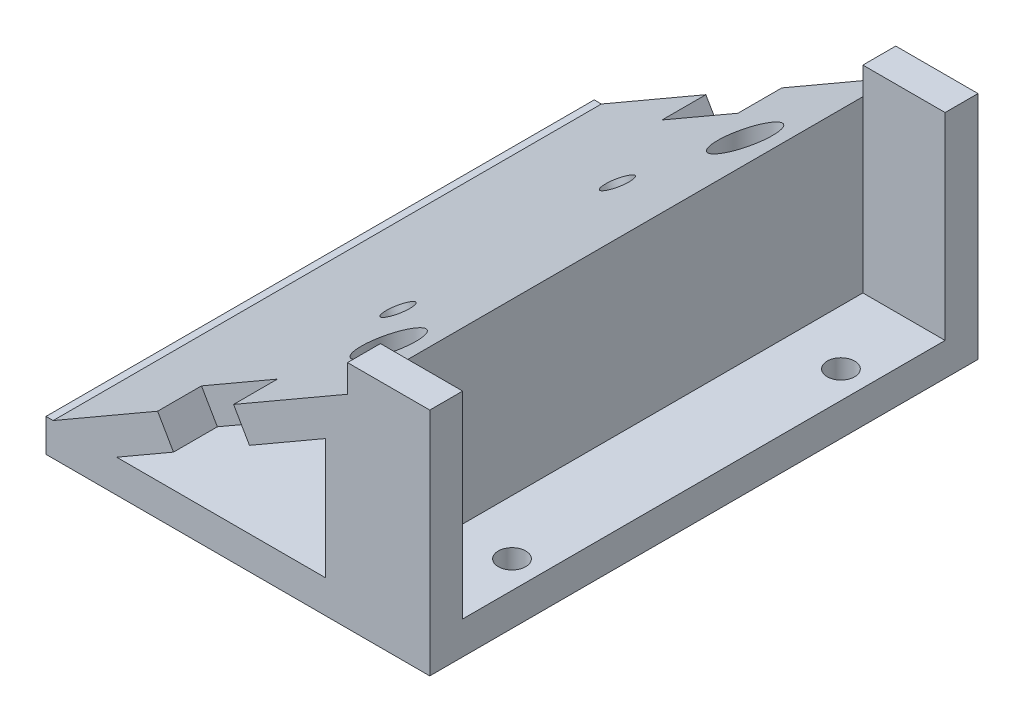
SolidWorks part; units mm, degrees
ref_plane "Front Plane" through (0, 0, 0) normal (0, 0, 1) x (1, 0, 0)
ref_plane "Top Plane" through (0, 0, 0) normal (0, 1, 0) x (1, 0, 0)
ref_plane "Right Plane" through (0, 0, 0) normal (1, 0, 0) x (0, 0, -1)
sketch "Sketch1" plane through (0, 0, 0) normal (0, 1, 0) x (1, 0, 0)
  line L1 (-70.1234, 23.0109) -> (-105.1234, 23.0109)
  line L2 (-70.1234, 23.0109) -> (-70.1234, 73.0109)
  line L3 (-70.1234, 73.0109) -> (-105.1234, 73.0109)
  line L4 (-105.1234, 23.0109) -> (-105.1234, 73.0109)
  dimension "D1" = 50
  dimension "D2" = 35
extrude "Boss-Extrude1" add sketch "Sketch1" along normal blind 3
sketch "Sketch2" plane through (0, 3, 0) normal (0, 1, 0) x (1, 0, 0)
  line L0 (-70.1234, 73.0109) -> (-105.1234, 73.0109) construction
  line L1 (-70.1234, 23.0109) -> (-70.1234, 73.0109) construction
  line L2 (-105.1234, 23.0109) -> (-70.1234, 23.0109) construction
  circle A1 centre (-82.6234, 64.264) radius 1.5
  circle A2 centre (-82.6234, 31.764) radius 1.5
  circle A3 centre (-72.6234, 33.0109) radius 1.25
  circle A4 centre (-72.6234, 63.0109) radius 1.25
  dimension "D8" = 3
  dimension "D9" = 3
  dimension "D10" = 2.5
  dimension "D11" = 2.5
  dimension "D1" = 30
  dimension "D2" = 32.5
  dimension "D3" = 10
  dimension "D4" = 10
  dimension "D5" = 10
  dimension "D6" = 2.5
  dimension "D7" = 2.5
  dimension "D12" = 8.7531
extrude "Cut-Extrude1" cut sketch "Sketch2" against normal through all
sketch "Sketch4" plane through (0, 0, -23.0109) normal (0, 0, 1) x (1, 0, 0)
  line L0 (-77.6234, 3) -> (-104.4702, 3)
  line L2 (-104.4702, 3) -> (-77.6234, 18.5)
  line L3 (-77.6234, 18.5) -> (-77.6234, 3)
  line L7 (-105.1234, 3) -> (-70.1234, 3) construction
  line L8 (-70.1234, 3) -> (-70.1234, 0) construction
  dimension "D1" = 31
  dimension "D2" = 30
  dimension "D3" = 60
  dimension "D4" = 7.5
extrude "Boss-Extrude2" add sketch "Sketch4" against normal blind 50 contours L0 L2 L3
sketch "Sketch6" plane through (0, 0, -23.0109) normal (0, 0, 1) x (1, 0, 0)
  line L0 (-98.676, 3) -> (-79.6234, 3)
  line L2 (-98.676, 3) -> (-79.6234, 14)
  line L3 (-79.6234, 14) -> (-79.6234, 3)
  line L10 (-77.6234, 3) -> (-70.1234, 3) construction
  dimension "D1" = 30
  dimension "D2" = 60
  dimension "D3" = 2
  dimension "D4" = 22
extrude "Cut-Extrude5" cut sketch "Sketch6" against normal through all contours L0 L3 L2
sketch "Sketch8" plane through (0, 3, 0) normal (0, 1, 0) x (1, 0, 0)
  circle A0 centre (-82.6234, 31.764) radius 2.5
  circle A1 centre (-82.6234, 31.764) radius 1.5 construction
  circle A2 centre (-82.6234, 64.264) radius 2.5
  circle A3 centre (-82.6234, 64.264) radius 1.5 construction
  dimension "D1" = 5
  dimension "D2" = 5
extrude "Cut-Extrude6" cut sketch "Sketch8" against normal blind 1 and the other way through all
sketch "Sketch9" plane through (-27.4166, 47.4869, 0) normal (-0.5, 0.866, 0) x (0.866, 0.5, 0)
  line L0 (-88.9739, 73.0109) -> (-57.9739, 73.0109) construction
  line L1 (-57.9739, 73.0109) -> (-57.9739, 23.0109) construction
  circle A0 centre (-69.9739, 58.0109) radius 1.25
  circle A1 centre (-69.9739, 38.0109) radius 1.25
  dimension "D1" = 2.5
  dimension "D2" = 2.5
  dimension "D3" = 20
  dimension "D4" = 15
  dimension "D5" = 12
  dimension "D6" = 12
extrude "Cut-Extrude7" cut sketch "Sketch9" against normal up to next
sketch "Sketch10" plane through (-25.968, 44.978, 0) normal (0.5, -0.866, 0) x (-0.866, -0.5, 0)
  circle A0 centre (69.9739, 58.0109) radius 2.5
  circle A1 centre (69.9739, 38.0109) radius 2.5
  circle A3 centre (69.9739, 38.0109) radius 1.25 construction
  circle A4 centre (69.9739, 58.0109) radius 1.25 construction
  dimension "D1" = 5
  dimension "D2" = 5
extrude "Cut-Extrude8" cut sketch "Sketch10" against normal blind 0.5 and the other way up to next
sketch "Sketch11" plane through (0, 3, 0) normal (0, 1, 0) x (1, 0, 0)
  line L0 (-77.6234, 23.0109) -> (-70.1234, 23.0109) construction
  line L1 (-70.1234, 23.0109) -> (-77.6234, 23.0109)
  line L2 (-70.1234, 23.0109) -> (-70.1234, 26.0109)
  line L3 (-70.1234, 26.0109) -> (-77.6234, 26.0109)
  line L4 (-77.6234, 23.0109) -> (-77.6234, 26.0109)
  line L5 (-70.1234, 70.0109) -> (-77.6234, 70.0109)
  line L6 (-70.1234, 70.0109) -> (-70.1234, 73.0109)
  line L7 (-70.1234, 73.0109) -> (-77.6234, 73.0109)
  line L8 (-77.6234, 70.0109) -> (-77.6234, 73.0109)
  line L9 (-70.1234, 73.0109) -> (-77.6234, 73.0109) construction
  line L10 (-70.1234, 23.0109) -> (-70.1234, 73.0109) construction
  line L11 (-77.6234, 73.0109) -> (-77.6234, 23.0109) construction
  dimension "D1" = 3
  dimension "D2" = 3
  dimension "D3" = 0
  dimension "D4" = 0
  dimension "D5" = 0
  dimension "D6" = 0
  dimension "D7" = 0
  dimension "D8" = 0
extrude "Boss-Extrude3" add sketch "Sketch11" along normal blind 18
sketch "Sketch14" plane through (-27.4166, 47.4869, 0) normal (-0.5, 0.866, 0) x (0.866, 0.5, 0)
  line L0 (-88.9739, 73.0109) -> (-88.9739, 23.0109) construction
  line L1 (-77.9739, 23.0109) -> (-69.9739, 23.0109)
  line L2 (-77.9739, 23.0109) -> (-77.9739, 27.0109)
  line L3 (-77.9739, 27.0109) -> (-69.9739, 27.0109)
  line L4 (-69.9739, 23.0109) -> (-69.9739, 27.0109)
  line L5 (-88.9739, 23.0109) -> (-57.9739, 23.0109) construction
  line L6 (-77.9739, 69.0109) -> (-69.9739, 69.0109)
  line L7 (-77.9739, 69.0109) -> (-77.9739, 73.0109)
  line L8 (-77.9739, 73.0109) -> (-69.9739, 73.0109)
  line L9 (-69.9739, 69.0109) -> (-69.9739, 73.0109)
  line L10 (-88.9739, 73.0109) -> (-57.9739, 73.0109) construction
  dimension "D1" = 8
  dimension "D2" = 4
  dimension "D3" = 11
  dimension "D4" = 0
  dimension "D5" = 4
  dimension "D6" = 8
  dimension "D7" = 0
  dimension "D8" = 11
extrude "Cut-Extrude9" cut sketch "Sketch14" against normal up to next
